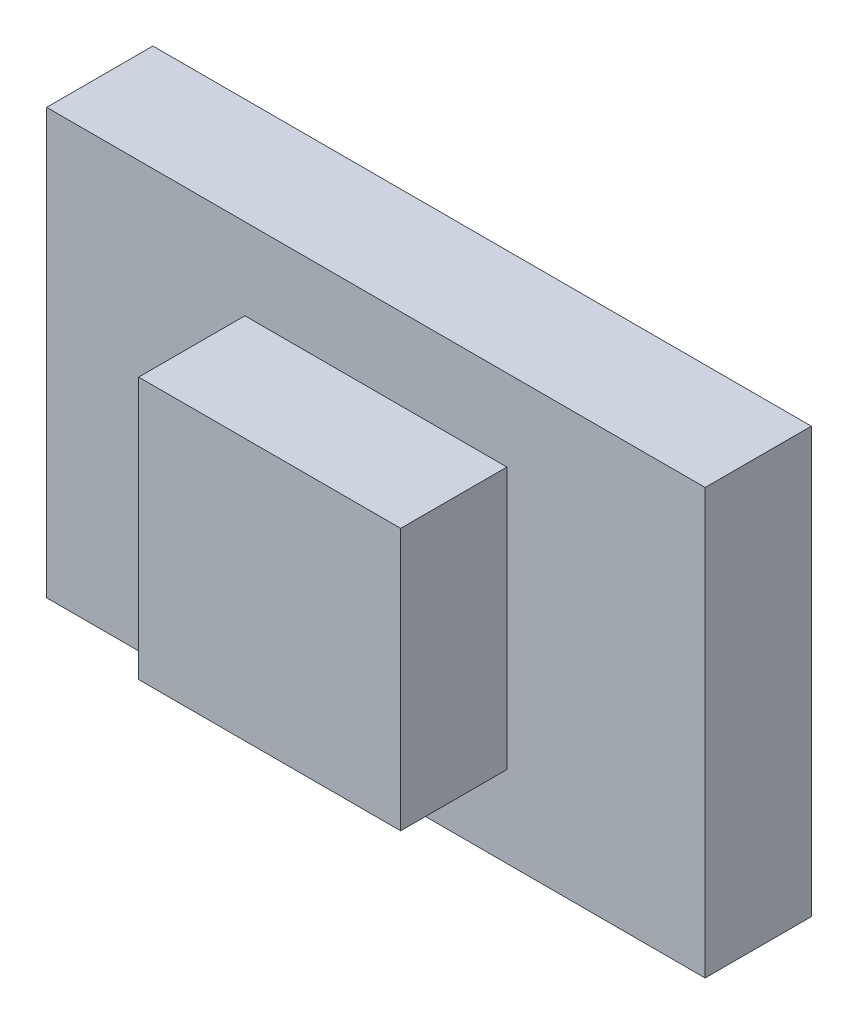
SolidWorks part; units mm, degrees
ref_plane "Front Plane" through (0, 0, 0) normal (1, 0, 0) x (0, 1, 0)
ref_plane "Top Plane" through (0, 0, 0) normal (0, 0, 1) x (0, 1, 0)
ref_plane "Right Plane" through (0, 0, 0) normal (0, 1, 0) x (-1, 0, 0)
sketch "Sketch1" plane through (0, 0, 0) normal (0, 0, 1) x (0, 1, 0)
  line L1 (30, -46.5) -> (-30, -46.5)
  line L2 (30, -46.5) -> (30, 46.5)
  line L3 (30, 46.5) -> (-30, 46.5)
  line L4 (-30, -46.5) -> (-30, 46.5)
  line L5 (30, -46.5) -> (-30, 46.5) construction
  line L6 (30, 46.5) -> (-30, -46.5) construction
  point P0 (0, 0)
  dimension "D1" = 60
  dimension "D2" = 93
extrude "Boss-Extrude1" add sketch "Sketch1" along normal blind 15
ref_plane "Plane1" through (0, 0, 15) normal (0, 0, 1) x (1, 0, 0)
sketch "Sketch2" plane through (0, 0, 15) normal (0, 0, 1) x (1, 0, 0)
  line L1 (18.5, 18.5) -> (-18.5, 18.5)
  line L2 (18.5, 18.5) -> (18.5, -18.5)
  line L3 (18.5, -18.5) -> (-18.5, -18.5)
  line L4 (-18.5, 18.5) -> (-18.5, -18.5)
  line L5 (18.5, 18.5) -> (-18.5, -18.5) construction
  line L6 (18.5, -18.5) -> (-18.5, 18.5) construction
  point P0 (0, 0)
  dimension "D1" = 37
  dimension "D2" = 37
extrude "Boss-Extrude2" add sketch "Sketch2" along normal blind 15
